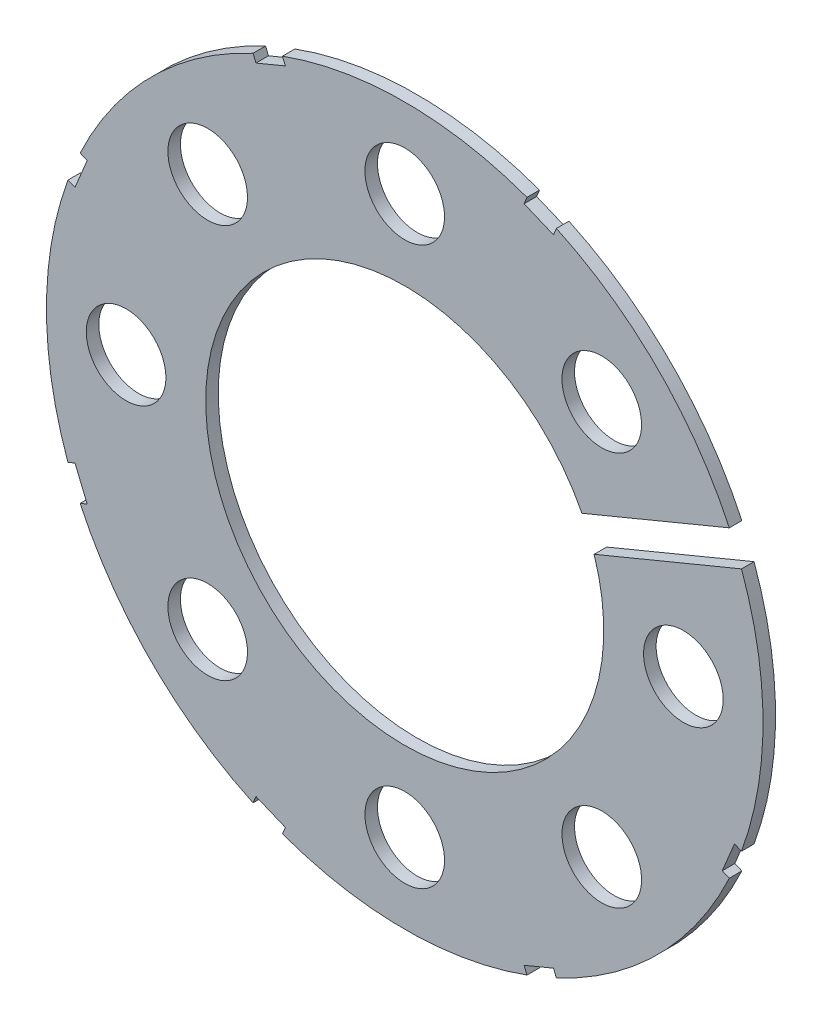
SolidWorks part; units mm, degrees
material "Copper"
ref_plane "Front Plane" through (0, 0, 0) normal (0, 0, 1) x (1, 0, 0)
ref_plane "Top Plane" through (0, 0, 0) normal (0, 1, 0) x (1, 0, 0)
ref_plane "Right Plane" through (0, 0, 0) normal (1, 0, 0) x (0, 0, -1)
sketch "Sketch4" plane through (0, 0, 0) normal (0, 0, 1) x (1, 0, 0)
  circle A0 centre (0, 0) radius 28.575
  dimension "D1" = 57.15
extrude "Boss-Extrude2" add sketch "Sketch4" along normal blind 1
sketch "Sketch5" plane through (0, 0, 1) normal (0, 0, 1) x (1, 0, 0)
  circle A0 centre (0, 0) radius 15.875
  circle A1 centre (0, 0) radius 28.575 construction
  dimension "D2" = 12.7
extrude "Cut-Extrude5" cut sketch "Sketch5" against normal through all
sketch "Sketch6" plane through (0, 0, 1) normal (0, 0, 1) x (1, 0, 0)
  circle A0 centre (22.225, 0) radius 3.175
  circle A4 centre (0, 0) radius 28.575 construction
  dimension "D2" = 6.35
  dimension "D1" = 6.35
extrude "Cut-Extrude6" cut sketch "Sketch6" against normal through all
pattern_circular "CirPattern1" count 8 over 360 about axis through (0, 0, 0) along (0, 0, 1) of "Cut-Extrude6"
sketch "Sketch8" plane through (0, 0, 1) normal (0, 0, 1) x (1, 0, 0)
  line L0 (29.4338, 13.5665) -> (10.6606, 5.7904)
  line L1 (29.4338, 13.5665) -> (30.4058, 11.2199)
  line L2 (10.6606, 5.7904) -> (11.6326, 3.4437)
  line L3 (30.4058, 11.2199) -> (11.6326, 3.4437)
  line L4 (29.4338, 13.5665) -> (11.6326, 3.4437) construction
  line L5 (10.6606, 5.7904) -> (30.4058, 11.2199) construction
  line L6 (0, 0) -> (50.4438, 0) construction
  line L7 (12.3515, 26.5005) -> (10.0049, 27.4725)
  line L8 (12.3515, 26.5005) -> (11.8655, 25.3272)
  line L9 (10.0049, 27.4725) -> (9.5188, 26.2992)
  line L10 (11.8655, 25.3272) -> (9.5188, 26.2992)
  line L11 (10.0049, 27.4725) -> (11.8655, 25.3272) construction
  line L12 (12.3515, 26.5005) -> (9.5188, 26.2992) construction
  line L13 (-10.0049, 27.4725) -> (-12.3515, 26.5005)
  line L14 (-10.0049, 27.4725) -> (-9.5188, 26.2992)
  line L15 (-9.5188, 26.2992) -> (-11.8655, 25.3272)
  line L16 (-12.3515, 26.5005) -> (-11.8655, 25.3272)
  line L17 (-10.0049, 27.4725) -> (-11.8655, 25.3272) construction
  line L18 (-12.3515, 26.5005) -> (-9.5188, 26.2992) construction
  line L19 (-26.5005, 12.3515) -> (-27.4725, 10.0049)
  line L20 (-26.5005, 12.3515) -> (-25.3272, 11.8655)
  line L21 (-25.3272, 11.8655) -> (-26.2992, 9.5188)
  line L22 (-27.4725, 10.0049) -> (-26.2992, 9.5188)
  line L23 (-26.5005, 12.3515) -> (-26.2992, 9.5188) construction
  line L24 (-27.4725, 10.0049) -> (-25.3272, 11.8655) construction
  line L25 (-27.4725, -10.0049) -> (-26.5005, -12.3515)
  line L26 (-27.4725, -10.0049) -> (-26.2992, -9.5188)
  line L27 (-26.2992, -9.5188) -> (-25.3272, -11.8655)
  line L28 (-26.5005, -12.3515) -> (-25.3272, -11.8655)
  line L29 (-27.4725, -10.0049) -> (-25.3272, -11.8655) construction
  line L30 (-26.5005, -12.3515) -> (-26.2992, -9.5188) construction
  line L31 (-12.3515, -26.5005) -> (-10.0049, -27.4725)
  line L32 (-12.3515, -26.5005) -> (-11.8655, -25.3272)
  line L33 (-11.8655, -25.3272) -> (-9.5188, -26.2992)
  line L34 (-10.0049, -27.4725) -> (-9.5188, -26.2992)
  line L35 (-12.3515, -26.5005) -> (-9.5188, -26.2992) construction
  line L36 (-10.0049, -27.4725) -> (-11.8655, -25.3272) construction
  line L37 (10.0049, -27.4725) -> (12.3515, -26.5005)
  line L38 (10.0049, -27.4725) -> (9.5188, -26.2992)
  line L39 (9.5188, -26.2992) -> (11.8655, -25.3272)
  line L40 (12.3515, -26.5005) -> (11.8655, -25.3272)
  line L41 (10.0049, -27.4725) -> (11.8655, -25.3272) construction
  line L42 (12.3515, -26.5005) -> (9.5188, -26.2992) construction
  line L43 (26.5005, -12.3515) -> (27.4725, -10.0049)
  line L44 (26.5005, -12.3515) -> (25.3272, -11.8655)
  line L45 (25.3272, -11.8655) -> (26.2992, -9.5188)
  line L46 (27.4725, -10.0049) -> (26.2992, -9.5188)
  line L47 (26.5005, -12.3515) -> (26.2992, -9.5188) construction
  line L48 (27.4725, -10.0049) -> (25.3272, -11.8655) construction
  circle A0 centre (0, 0) radius 28.575 construction
  point P1 (20.5332, 8.5051)
  point P3 (10.9352, 26.3999)
  point P11 (-10.9352, 26.3999)
  point P20 (-26.3999, 10.9352)
  point P25 (-26.3999, -10.9352)
  point P26 (0, 0)
  point P31 (-10.9352, -26.3999)
  point P36 (10.9352, -26.3999)
  point P41 (26.3999, -10.9352)
  point P46 (0, 0)
  dimension "D1" = 20.32
  dimension "D2" = 6.35
  dimension "D3" = 2.54
  dimension "D4" = 22.5
  dimension "D5" = 1.27
  dimension "D6" = 2.54
  dimension "D7" = 1.27
  dimension "D8" = 1.27
  dimension "D9" = 0.635
  dimension "D10" = 67.5
  dimension "D11" = 7
extrude "Cut-Extrude11" cut sketch "Sketch8" against normal through all
